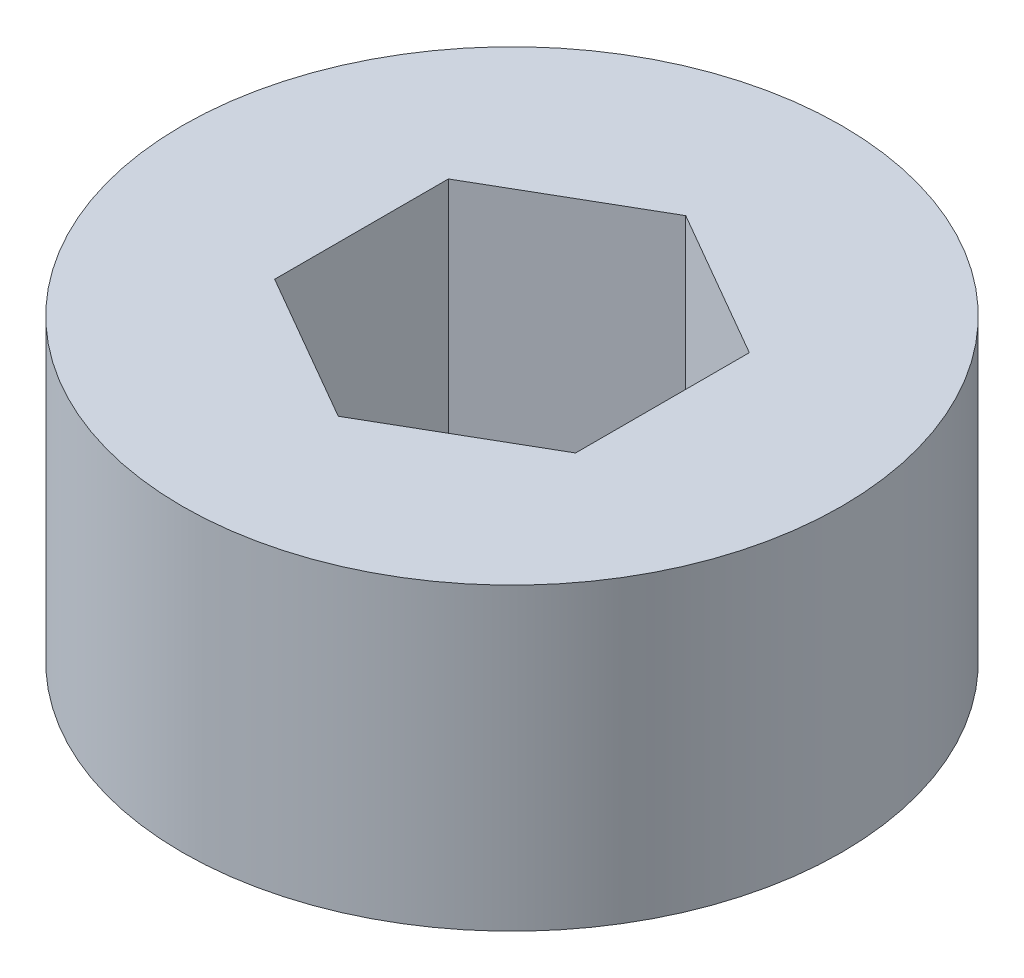
SolidWorks part; units mm, degrees
ref_plane "Front Plane" through (0, 0, 0) normal (0, 0, 1) x (1, 0, 0)
ref_plane "Top Plane" through (0, 0, 0) normal (0, 1, 0) x (1, 0, 0)
ref_plane "Right Plane" through (0, 0, 0) normal (1, 0, 0) x (0, 0, -1)
sketch "Sketch1" plane through (0, 0, 0) normal (0, 1, 0) x (1, 0, 0)
  circle A0 centre (0, 0) radius 13.97
  dimension "D1" = 27.94
extrude "Boss-Extrude1" add sketch "Sketch1" along normal blind 12.7
sketch "Sketch2" plane through (0, 12.7, 0) normal (0, 1, 0) x (1, 0, 0)
  line L0 (0, 0) -> (0, 7.3617) construction
  line L1 (0, 7.3617) -> (-6.3754, 3.6808)
  line L2 (-6.3754, 3.6808) -> (-6.3754, -3.6808)
  line L3 (-6.3754, -3.6808) -> (0, -7.3617)
  line L4 (0, -7.3617) -> (6.3754, -3.6808)
  line L5 (6.3754, -3.6808) -> (6.3754, 3.6808)
  line L6 (6.3754, 3.6808) -> (0, 7.3617)
  circle A0 centre (0, 0) radius 6.3754 construction
  dimension "D1" = 12.7508
extrude "Cut-Extrude1" cut sketch "Sketch2" against normal blind 12.7
sketch "Sketch3" plane through (0, 12.7, 0) normal (0, 1, 0) x (1, 0, 0)
  circle A0 centre (0, 0) radius 10.795
  dimension "D1" = 21.59
